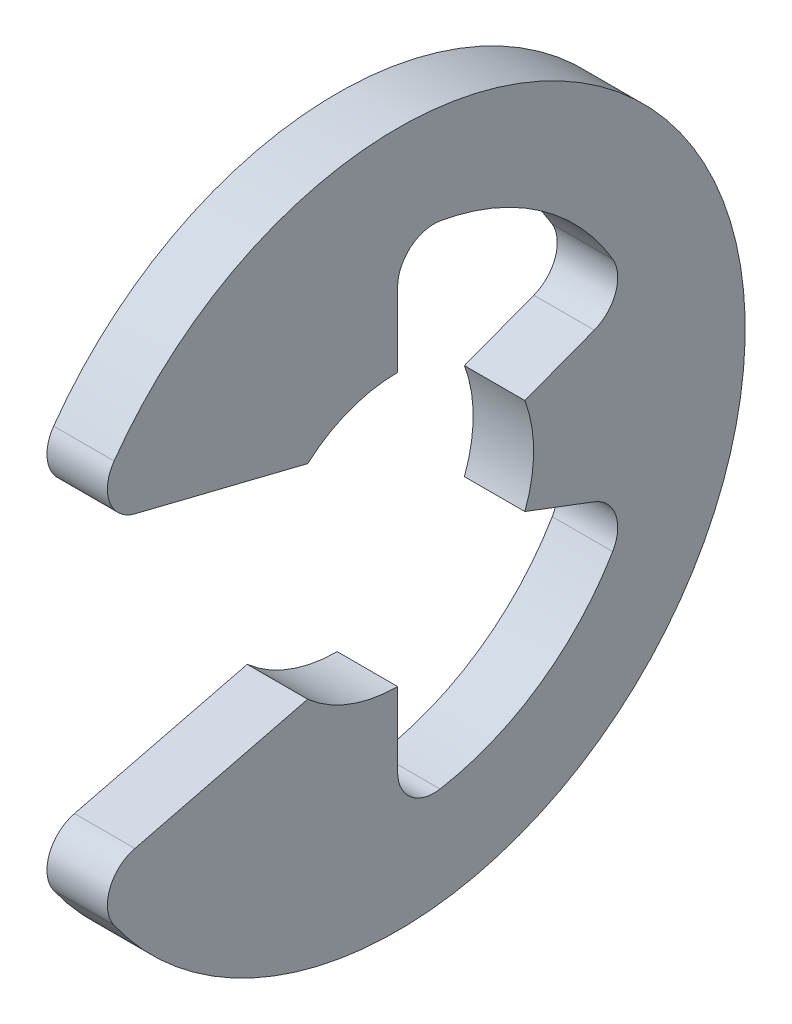
SolidWorks part; units mm, degrees
ref_plane "Front" through (0, 0, 0) normal (0, 0, 1) x (1, 0, 0)
ref_plane "Top" through (0, 0, 0) normal (0, 1, 0) x (1, 0, 0)
ref_plane "Right" through (0, 0, 0) normal (1, 0, 0) x (0, 0, -1)
sketch "Sketch1" plane through (0, 0, 0) normal (1, 0, 0) x (0, 0, -1)
  line L0 (-3.0795, -1.5554) -> (-0.8929, -1.0125)
  line L1 (-3.0795, 1.5554) -> (-0.8929, 1.0125)
  line L2 (0, -1.35) -> (0, -2.4774)
  line L3 (0, 1.35) -> (0, 2.4774)
  line L4 (1.2628, -0.4773) -> (2.3174, -0.8759)
  line L5 (1.2628, 0.4773) -> (2.3174, 0.8759)
  line L6 (0, 0) -> (-3.65, 0) construction
  line L7 (1.2628, 0.4773) -> (1.2628, -0.4773) construction
  line L8 (0, -1.35) -> (-0.8929, -1.0125) construction
  circle A1 centre (0, 0) radius 3.65 construction
  circle A2 centre (0, 0) radius 1.35 construction
  arc A3 (-3.0795, -1.5554) -> (-3.0795, 1.5554) centre (0, 0) ccw
  arc A4 (-0.8929, -1.0125) -> (0, -1.35) centre (0, 0) ccw
  arc A5 (-0.8929, 1.0125) -> (0, 1.35) centre (0, 0) cw
  arc A6 (1.2628, 0.4773) -> (1.2628, -0.4773) centre (0, 0) cw
  arc A7 (0, -2.4774) -> (2.3174, -0.8759) centre (0, 0) ccw
  arc A8 (2.3174, 0.8759) -> (0, 2.4774) centre (0, 0) ccw
  dimension "D" = 2.7
  dimension "D1" = 2.4774
  dimension "OD" = 6.9
  dimension "D2" = 1.535
  dimension "D3" = 2.025
extrude "Extrude1" add sketch "Sketch1" along normal mid plane 0.6
fillet "Fillet1" radius 0.36 6 edges at (0, -2.4774, 0) (0, 2.4774, 0) (0, -1.5554, 3.0795) (0, 1.5554, 3.0795) (0, -0.8759, -2.3174) (0, 0.8759, -2.3174)
sketch "Sketch3" plane through (0, 0, 0) normal (0, 1, 0) x (1, 0, 0)
  line L0 (0.32, 2) -> (0.32, 1.6)
  line L1 (0.32, 1.6) -> (-0.32, 1.6)
  line L2 (-0.32, 1.6) -> (-0.32, 2)
  line L3 (-0.32, 2) -> (-4.48, 2)
  line L4 (1.92, 0) -> (1.92, 1.8)
  line L5 (-4.48, 2) -> (-4.48, 0)
  line L6 (-4.48, 0) -> (1.92, 0)
  line L8 (1.92, 0) -> (1.92, 2) construction
  line L9 (1.92, 2) -> (0.32, 2) construction
  line L10 (1.92, 0) -> (17.2631, 0) construction
  line L11 (1.92, 1.8) -> (1.72, 2)
  line L12 (1.72, 2) -> (0.32, 2)
  point P2 (0, 1.6)
  point P5 (0.32, 1.8)
  dimension "D2" = 6.4
  dimension "D1" = 1.6
  dimension "D3" = 45
revolve "Revolve2" [suppressed] add sketch "Sketch3" angle 360 about L10
equation "\"D2@Sketch3\" = \"W@Sketch3\"*10"
equation "\"D1@Sketch3\" = \"D2@Sketch3\"/4"
equation "\"D1@Sketch1\" = (\"OD@Sketch1\"+\"D@Sketch1\")/3.875"
equation "\"D3@Sketch1\" = \"D@Sketch1\"*.75"
equation "\"D1@Fillet1\" = \"D1@Extrude1\"*.6"
